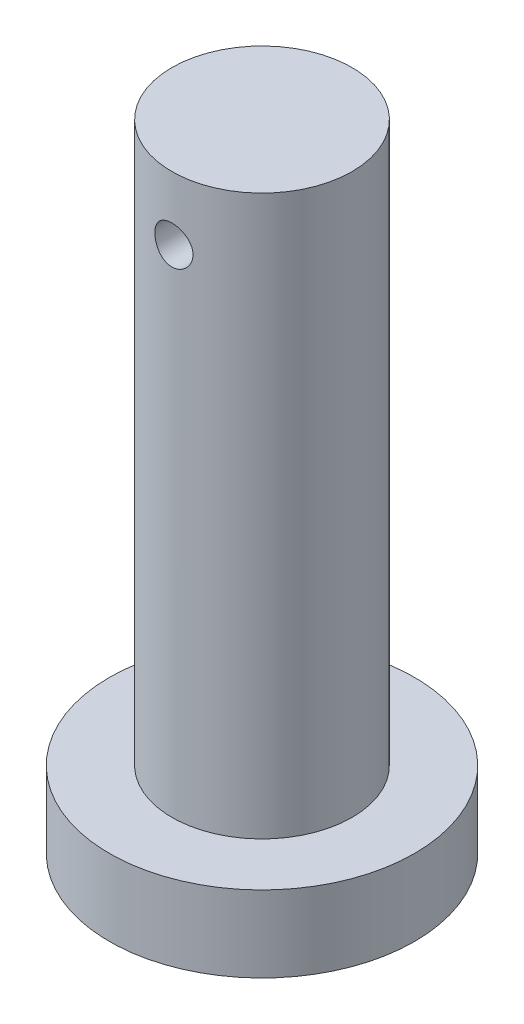
SolidWorks part; units mm, degrees
material "Galvanized Steel"
ref_plane "Front Plane" through (0, 0, 0) normal (0, 0, 1) x (1, 0, 0)
ref_plane "Top Plane" through (0, 0, 0) normal (0, 1, 0) x (1, 0, 0)
ref_plane "Right Plane" through (0, 0, 0) normal (1, 0, 0) x (0, 0, -1)
sketch "Sketch2" plane through (0, 0, 0) normal (0, 0, 1) x (1, 0, 0)
  line L0 (0, 0) -> (30, 0)
  line L1 (30, 0) -> (30, 15)
  line L2 (30, 15) -> (17.7222, 15)
  line L3 (17.7222, 15) -> (17.7222, 125)
  line L4 (17.7222, 125) -> (0, 125)
  line L5 (0, 125) -> (0, 0)
  dimension "D1" = 30
  dimension "D2" = 15
  dimension "D3" = 110
  dimension "D4" = 17.7222
revolve "Revolve1" add sketch "Sketch2" angle 360 about L5
sketch "Sketch3" plane through (0, 0, 0) normal (0, 0, 1) x (1, 0, 0)
  line L0 (17.7222, 125) -> (-17.7222, 125) construction
  line L1 (17.7222, 125) -> (-17.7222, 125) construction
  line L2 (0, 125) -> (0, 112.5) construction
  circle A0 centre (0, 112.5) radius 3.75
  dimension "D2" = 7.5
  dimension "D1" = 12.5
extrude "Cut-Extrude1" cut sketch "Sketch3" against normal through all both and the other way through all
equation "\"D3@Sketch2\"=90+\"D2@Sketch2\"+5"
equation "\"D4@Sketch2\"=35.4444/2"
equation "\"D1@Sketch3\"=5+(15/2)"
